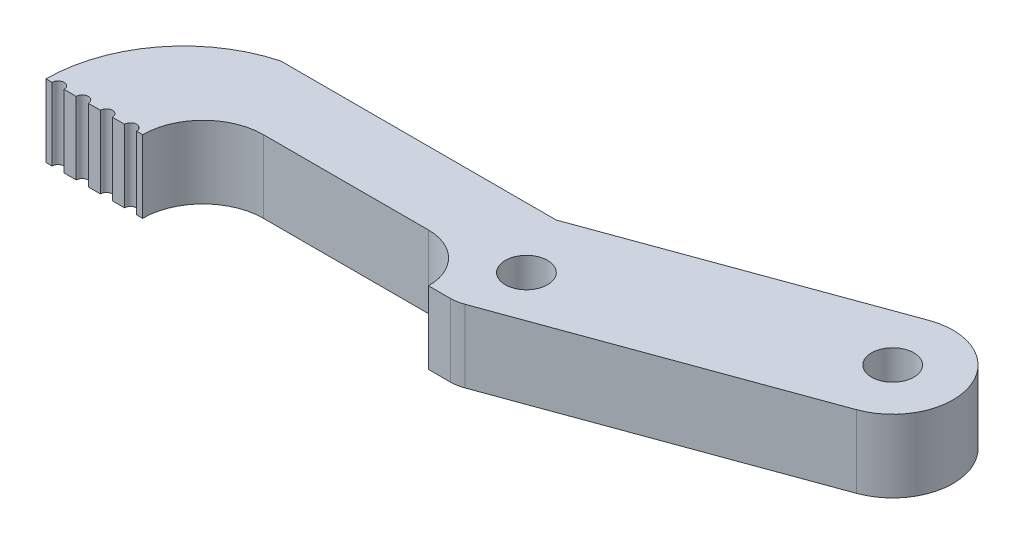
SolidWorks part; units mm, degrees
material "PET"
ref_plane "Спереди" through (0, 0, 0) normal (0, 0, 1) x (1, 0, 0)
ref_plane "Сверху" through (0, 0, 0) normal (0, 1, 0) x (1, 0, 0)
ref_plane "Справа" through (0, 0, 0) normal (1, 0, 0) x (0, 0, -1)
sketch "Эскиз1" plane through (0, 0, 0) normal (0, 1, 0) x (1, 0, 0)
  line L0 (-3.9917, 0) -> (4.0083, 0)
  line L1 (9.0083, 5) -> (22.6818, 5)
  line L2 (4.4451, 11) -> (27.2451, 11)
  line L3 (27.2451, 11) -> (49.8604, 19.2313)
  line L4 (29.0083, 1) -> (53.2807, 9.8344)
  line L6 (26.6818, 1) -> (29.0083, 1)
  arc A0 (4.0083, 0) -> (9.0083, 5) centre (9.0083, 0) cw
  arc A2 (-3.9917, 0) -> (4.4451, 11) centre (7.3977, 0) cw
  arc A4 (53.2807, 9.8344) -> (49.8604, 19.2313) centre (51.5705, 14.5329) ccw
  arc A5 (22.6818, 5) -> (26.6818, 1) centre (22.6818, 1) cw
  circle A6 centre (51.5705, 14.5329) radius 1.75
  circle A7 centre (29.7818, 6) radius 1.75
  point P18 (15.8451, 11)
  point P19 (15.8451, 5)
  dimension "D1" = 22.8
  dimension "D9" = 3.1
  dimension "D7" = 3.5
  dimension "D11" = 3.5
  dimension "D2" = 8
  dimension "D3" = 6
  dimension "D4" = 10
  dimension "D5" = 10
  dimension "D6" = 11
  dimension "D8" = 160
  dimension "D10" = 5
  dimension "D12" = 33
  dimension "D13" = 23.4
extrude "Бобышка-Вытянуть1" add sketch "Эскиз1" along normal blind 6
fillet "Скругление1" radius 3 1 edges at (29.0083, 3, -1)
sketch "Эскиз2" plane through (0, 6, 0) normal (0, 1, 0) x (1, 0, 0)
  line L0 (0.0083, 0) -> (0.0083, 1.0173) construction
  line L1 (-3.9917, 0) -> (4.0083, 0) construction
  circle A0 centre (1.0083, 0) radius 0.5
  circle A2 centre (3.0083, 0) radius 0.5
  circle A3 centre (-0.9917, 0) radius 0.5
  circle A4 centre (-2.9917, 0) radius 0.5
  dimension "D1" = 1
  dimension "D2" = 2
  dimension "D3" = 1
extrude "Вырез-Вытянуть1" cut sketch "Эскиз2" against normal through all
